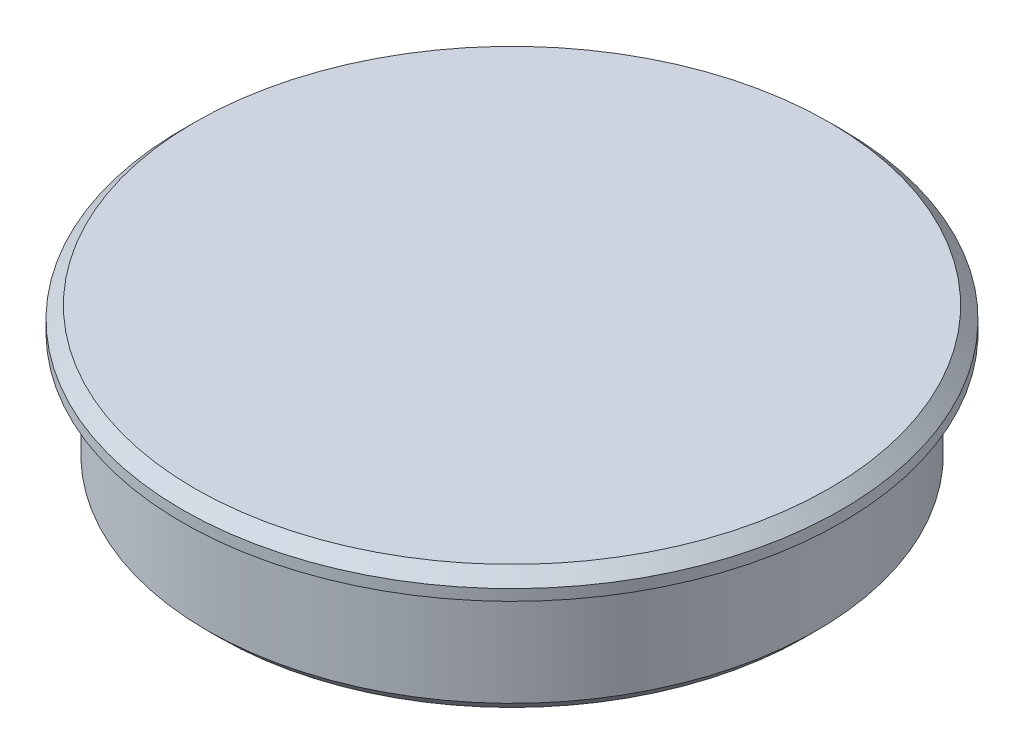
SolidWorks part; units mm, degrees
material "Brass"
ref_plane "Front" through (0, 0, 0) normal (0, 0, 1) x (1, 0, 0)
ref_plane "Top" through (0, 0, 0) normal (0, 1, 0) x (1, 0, 0)
ref_plane "Right" through (0, 0, 0) normal (1, 0, 0) x (0, 0, -1)
sketch "Sketch2" plane through (0, 0, 0) normal (0, 0, 1) x (1, 0, 0)
  line L0 (12.4079, -3.75) -> (10.4079, -3.75)
  line L1 (10.4079, -3.75) -> (10.4079, 0)
  line L2 (10.4079, 0) -> (0, 0)
  line L3 (0, 0) -> (0, 2)
  line L4 (0, 2) -> (13.4079, 2)
  line L5 (13.4079, 2) -> (13.4079, 1.05)
  line L6 (13.4079, 1.05) -> (12.4079, 1.05)
  line L7 (12.4079, 1.05) -> (12.4079, -3.75)
  line L8 (0, 0) -> (0, 31.3021) construction
  dimension "D1" = 2
  dimension "D2" = 4.8
  dimension "D3" = 24.8158
  dimension "D4" = 2
  dimension "D5" = 0.95
  dimension "D6" = 1
revolve "Revolve1" add sketch "Sketch2" angle 360 about L8
chamfer "Chamfer1" distance 0.5 angle 45 2 edges at (0, -3.75, -12.4079) (0, 2, -13.4079)
